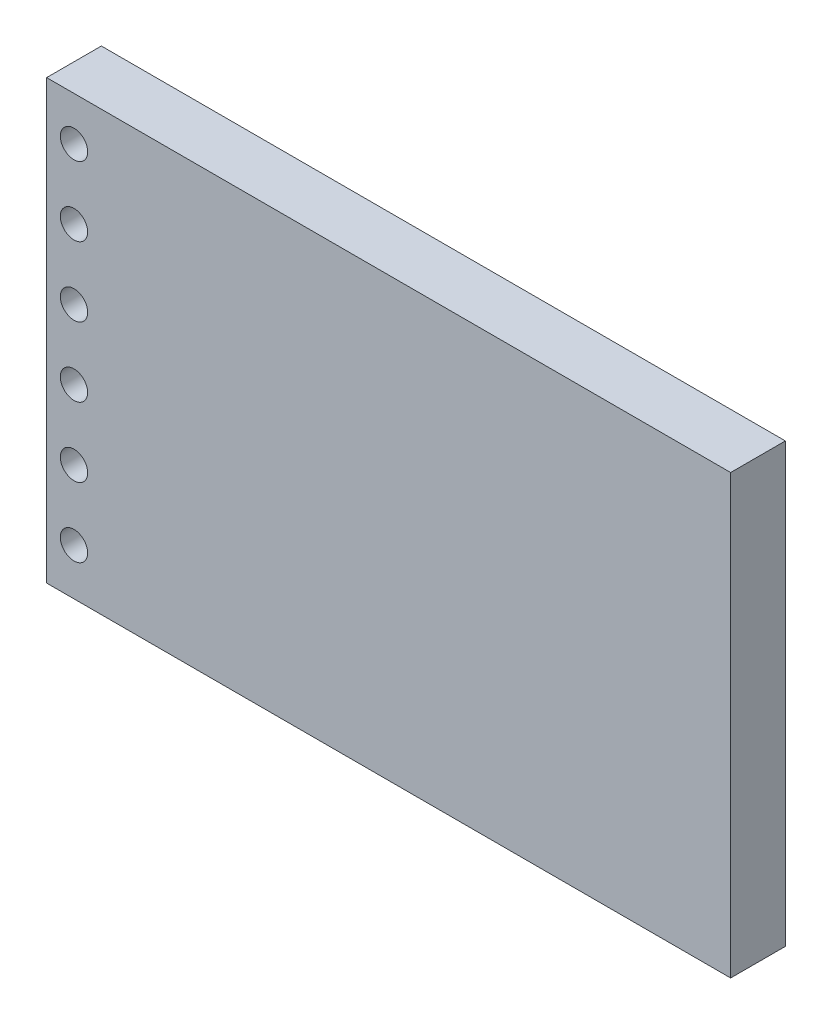
SolidWorks part; units mm, degrees
ref_plane "前视基准面" through (0, 0, 0) normal (0, 0, 1) x (1, 0, 0)
ref_plane "上视基准面" through (0, 0, 0) normal (0, 1, 0) x (1, 0, 0)
ref_plane "右视基准面" through (0, 0, 0) normal (1, 0, 0) x (0, 0, -1)
other "Configuration Table"
sketch "草图1" plane through (0, 0, 0) normal (0, 0, 1) x (1, 0, 0)
  line L1 (0, 0) -> (25, 0)
  line L2 (0, 0) -> (0, 16)
  line L3 (0, 16) -> (25, 16)
  line L4 (25, 0) -> (25, 16)
  dimension "D1" = 25
  dimension "D2" = 16
extrude "凸台-拉伸1" add sketch "草图1" along normal blind 2
sketch "草图2" plane through (0, 0, 0) normal (0, 0, -1) x (-1, 0, 0)
  line L0 (-25, 16) -> (0, 16) construction
  line L1 (0, 16) -> (0, 0) construction
  circle A0 centre (-1, 14.4) radius 0.5
  circle A1 centre (-1, 11.86) radius 0.5
  circle A2 centre (-1, 9.32) radius 0.5
  circle A3 centre (-1, 6.78) radius 0.5
  circle A4 centre (-1, 4.24) radius 0.5
  circle A5 centre (-1, 1.7) radius 0.5
  dimension "D1" = 1
  dimension "D3" = 1.6
  dimension "D4" = 1
  dimension "D2" = 6
extrude "切除-拉伸1" cut sketch "草图2" against normal through all
sketch "草图3" plane through (0, 0, 0) normal (0, 0, -1) x (-1, 0, 0)
  line L0 (-25, 0) -> (-25, 16) construction
  line L1 (-23.7998, 10.5) -> (-21.8013, 10.5)
  line L2 (-23.7998, 10.5) -> (-23.7998, 9.5)
  line L3 (-23.7998, 9.5) -> (-21.8013, 9.5)
  line L4 (-21.8013, 10.5) -> (-21.8013, 9.5)
  line L9 (-25, 16) -> (0, 16) construction
  line L10 (-23.7998, 8.5) -> (-21.8013, 8.5)
  line L11 (-21.8013, 8.5) -> (-21.8013, 7.5)
  line L12 (-23.7998, 7.5) -> (-21.8013, 7.5)
  line L13 (-23.7998, 8.5) -> (-23.7998, 7.5)
  line L14 (-23.7998, 6.5) -> (-21.8013, 6.5)
  line L15 (-21.8013, 6.5) -> (-21.8013, 5.5)
  line L16 (-23.7998, 5.5) -> (-21.8013, 5.5)
  line L17 (-23.7998, 6.5) -> (-23.7998, 5.5)
  line L18 (-23.7998, 4.5) -> (-21.8013, 4.5)
  line L19 (-21.8013, 4.5) -> (-21.8013, 3.5)
  line L20 (-23.7998, 3.5) -> (-21.8013, 3.5)
  line L21 (-23.7998, 4.5) -> (-23.7998, 3.5)
  dimension "D1" = 1.9984
  dimension "D2" = 1
  dimension "D3" = 1.2002
  dimension "D4" = 5.5
  dimension "D6" = 1
  dimension "D5" = 4
extrude "凸台-拉伸2" add sketch "草图3" along normal blind 0.5
sketch "草图4" plane through (0, 0, 0) normal (0, 0, -1) x (-1, 0, 0)
  line L0 (0, 0) -> (-25, 0) construction
  line L1 (-22, 0) -> (-18, 0)
  line L2 (-22, 0) -> (-22, 2)
  line L3 (-22, 2) -> (-18, 2)
  line L4 (-18, 0) -> (-18, 2)
  line L5 (-25, 0) -> (-25, 16) construction
  dimension "D1" = 3
  dimension "D2" = 2
  dimension "D3" = 4
extrude "凸台-拉伸3" add sketch "草图4" along normal blind 2
sketch "草图5" plane through (0, 0, 0) normal (0, -1, 0) x (1, 0, 0)
  line L0 (0, 2) -> (25, 2) construction
  line L1 (19.1141, -0.3095) -> (20.8828, -0.3095)
  line L2 (19.1141, -0.3095) -> (19.1141, -1.3685)
  line L3 (19.1141, -1.3685) -> (20.8828, -1.3685)
  line L4 (20.8828, -0.3095) -> (20.8828, -1.3685)
  line L5 (22, -2) -> (22, 0) construction
  line L6 (18, -2) -> (18, 0) construction
  line L7 (22, -2) -> (18, -2) construction
  dimension "D1" = 2.3095
  dimension "D2" = 1.1172
  dimension "D3" = 1.1141
  dimension "D4" = 0.6315
extrude "凸台-拉伸4" add sketch "草图5" along normal blind 1
